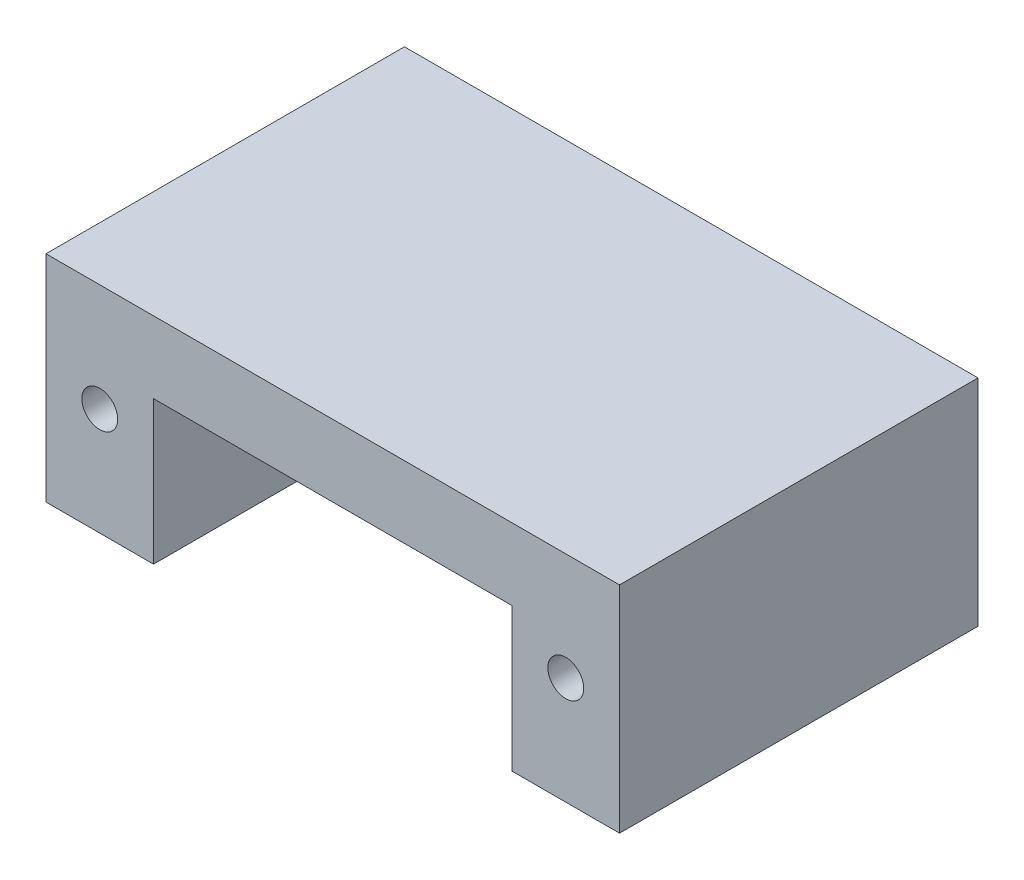
SolidWorks part; units mm, degrees
material "5052-H32"
ref_plane "Front Plane" through (0, 0, 0) normal (0, 0, 1) x (1, 0, 0)
ref_plane "Top Plane" through (0, 0, 0) normal (0, 1, 0) x (1, 0, 0)
ref_plane "Right Plane" through (0, 0, 0) normal (1, 0, 0) x (0, 0, -1)
sketch "Sketch1" plane through (0, 0, 0) normal (0, 0, 1) x (1, 0, 0)
  line L1 (-40, 15) -> (40, 15)
  line L2 (-40, 15) -> (-40, -15)
  line L3 (-40, -15) -> (40, -15)
  line L4 (40, 15) -> (40, -15)
  line L5 (-40, 15) -> (40, -15) construction
  line L6 (-40, -15) -> (40, 15) construction
  point P0 (0, 0)
  dimension "D1" = 80
  dimension "D2" = 30
extrude "Boss-Extrude1" add sketch "Sketch1" along normal blind 50
sketch "Sketch2" plane through (0, 0, 50) normal (0, 0, 1) x (1, 0, 0)
  line L0 (-25, -15) -> (-25, 5)
  line L1 (-40, -15) -> (40, -15) construction
  line L2 (-25, 5) -> (25, 5)
  line L3 (25, 5) -> (25, -15)
  line L4 (25, -15) -> (-25, -15)
  point P4 (0, -15)
  dimension "D1" = 50
  dimension "D2" = 20
extrude "Cut-Extrude1" cut sketch "Sketch2" against normal blind 50
sketch "Sketch3" plane through (0, 0, 50) normal (0, 0, 1) x (1, 0, 0)
  line L2 (25, -15) -> (40, -15) construction
  line L3 (40, -15) -> (40, 15) construction
  line L4 (-40, 15) -> (-40, -15) construction
  line L5 (-40, -15) -> (-25, -15) construction
  circle A2 centre (-32.5, 0) radius 2.5
  circle A4 centre (32.5, 0) radius 2.5
  dimension "D1" = 5
  dimension "D2" = 5
  dimension "D3" = 15
  dimension "D4" = 7.5
  dimension "D5" = 7.5
  dimension "D6" = 15
extrude "Cut-Extrude2" cut sketch "Sketch3" against normal blind 50
